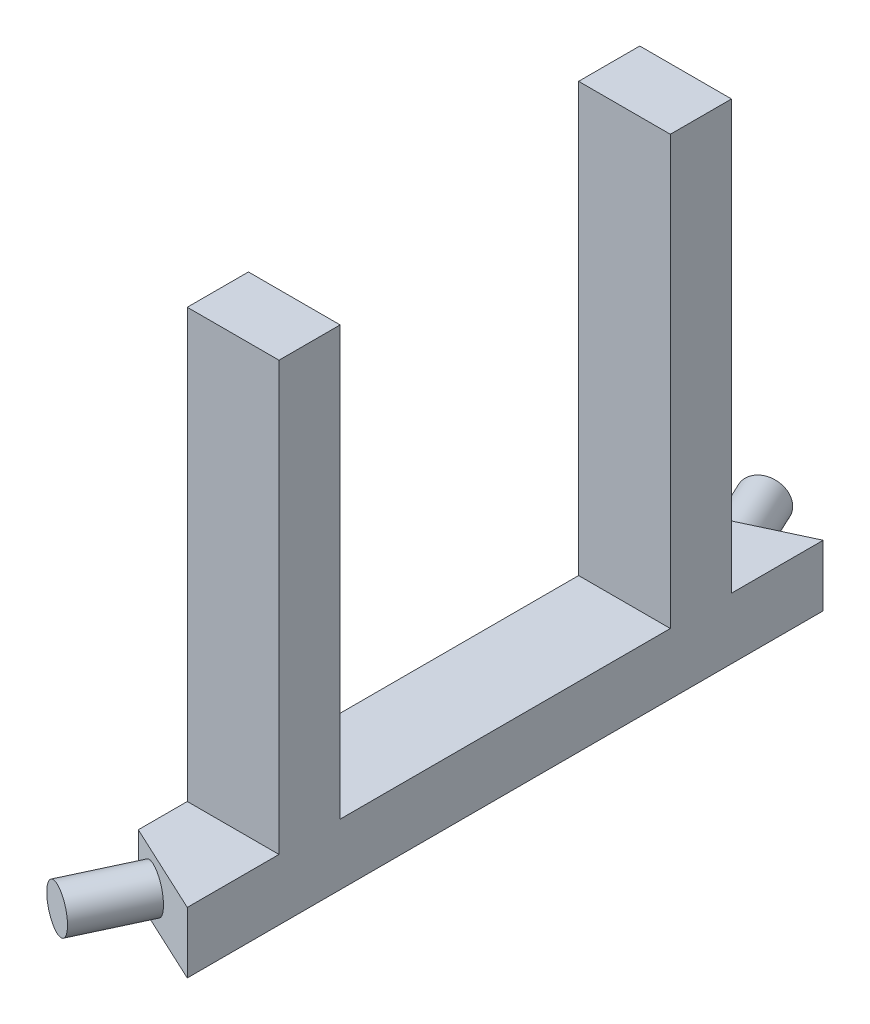
SolidWorks part; units mm, degrees
ref_plane "Front Plane" through (0, 0, 0) normal (0, 0, 1) x (1, 0, 0)
ref_plane "Top Plane" through (0, 0, 0) normal (0, 1, 0) x (1, 0, 0)
ref_plane "Right Plane" through (0, 0, 0) normal (1, 0, 0) x (0, 0, -1)
sketch "Sketch1" plane through (0, 0, 0) normal (0, 0, 1) x (1, 0, 0)
  line L1 (0, 0) -> (38.1, 0)
  line L2 (0, 0) -> (0, 25.4)
  line L3 (0, 25.4) -> (38.1, 25.4)
  line L4 (38.1, 0) -> (38.1, 25.4)
  dimension "D1" = 38.1
  dimension "D2" = 25.4
extrude "Boss-Extrude1" add sketch "Sketch1" along normal blind 132.08
sketch "Sketch5" plane through (0, 25.4, 0) normal (0, 1, 0) x (1, 0, 0)
  line L1 (38.1, -93.98) -> (0, -93.98)
  line L2 (38.1, -93.98) -> (38.1, -68.58)
  line L3 (38.1, -68.58) -> (0, -68.58)
  line L4 (0, -93.98) -> (0, -68.58)
  line L5 (38.1, -93.98) -> (0, -68.58) construction
  line L6 (38.1, -68.58) -> (0, -93.98) construction
  line L9 (0, -132.08) -> (0, 0) construction
  point P0 (38.1, -89.3782)
  dimension "D1" = 38.1
  dimension "D2" = 25.4
  dimension "D3" = 38.1
extrude "Boss-Extrude3" add sketch "Sketch5" along normal blind 177.8
sketch "Sketch2" plane through (0, 25.4, 0) normal (0, 1, 0) x (1, 0, 0)
  line L0 (-12.106, -108.6685) -> (38.1, -132.08)
  line L1 (38.1, -132.08) -> (38.1, -93.98) construction
  line L3 (-12.106, -108.6685) -> (-49.3863, -161.7657)
  line L4 (-49.3863, -161.7657) -> (54.8247, -172.4097)
  line L5 (54.8247, -172.4097) -> (38.1, -132.08)
  line L6 (38.1, -132.08) -> (0, -132.08) construction
  point P5 (0, -119.38)
  point P6 (0, 0)
  point P9 (0, -119.38)
  point P10 (0, 0)
  point P11 (0, 0)
  point P12 (0, 0)
  point P13 (0, 0)
  point P15 (-48.1909, -122.518)
  point P16 (0, -119.38)
  point P17 (-6.1747, -96.0852)
  point P18 (1.9274, -286.9314)
  point P19 (-51.3196, -157.5183)
  dimension "D1" = 25
extrude "Cut-Extrude1" cut sketch "Sketch2" against normal up to next (25.4 mm away)
mirror "Mirror2" about plane through (0, 0, 0) normal (0, 0, -1) of "Boss-Extrude1", "Boss-Extrude3", "Cut-Extrude1"
sketch "Sketch3" plane through (-43.7847, 0, 93.8965) normal (-0.4226, 0, 0.9063) x (0.9063, 0, 0.4226)
  line L1 (48.311, 0) -> (90.3497, 0) construction
  line L3 (48.311, 25.4) -> (48.311, 0) construction
  circle A0 centre (61.011, 12.7) radius 8.89
  dimension "D1" = 17.78
  dimension "D2" = 12.7
  dimension "D3" = 12.7
extrude "Boss-Extrude2" add sketch "Sketch3" along normal blind 30
mirror "Mirror3" about plane through (0, 0, 0) normal (0, 0, 1) of "Boss-Extrude2"
